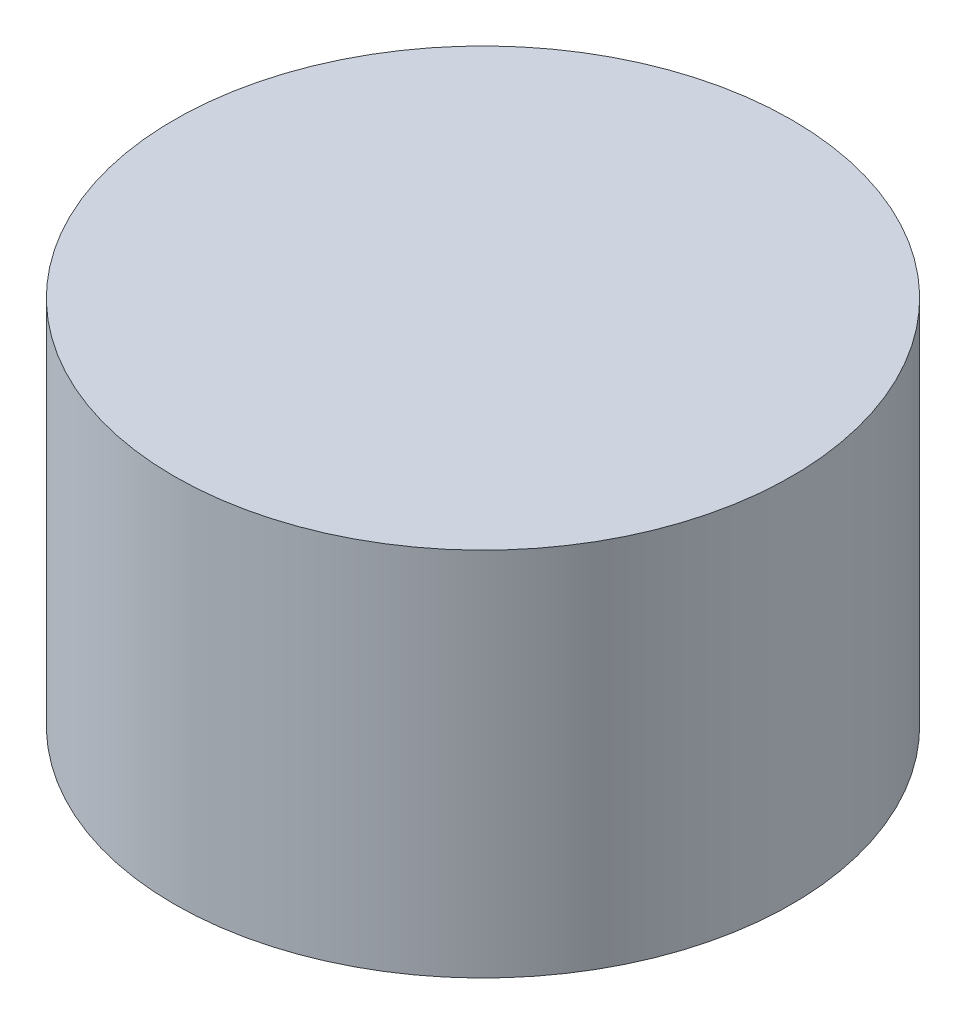
SolidWorks part; units mm, degrees
ref_plane "Plan de face" through (0, 0, 0) normal (0, 0, 1) x (1, 0, 0)
ref_plane "Plan de dessus" through (0, 0, 0) normal (0, 1, 0) x (1, 0, 0)
ref_plane "Plan de droite" through (0, 0, 0) normal (1, 0, 0) x (0, 0, -1)
sketch "Esquisse1" plane through (0, 0, 0) normal (0, 1, 0) x (1, 0, 0)
  circle A0 centre (0, 0) radius 0.5
extrude "Extrusion1" add sketch "Esquisse1" along normal blind 0.6
